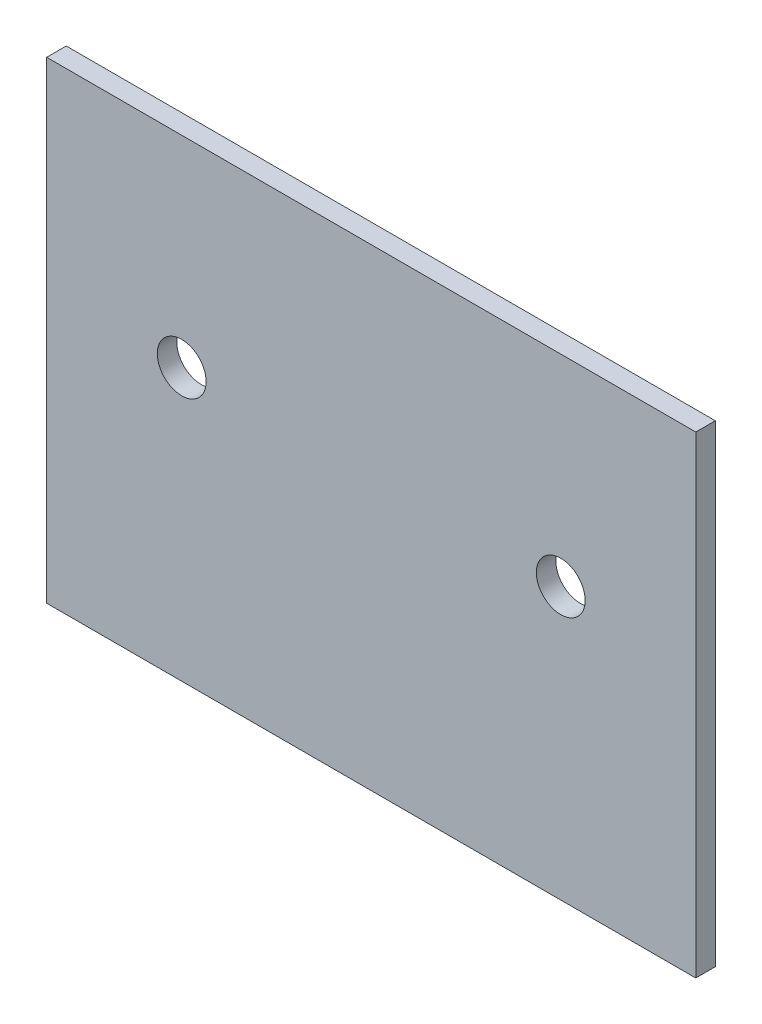
SolidWorks part; units mm, degrees
ref_plane "Front Plane" through (0, 0, 0) normal (0, 0, 1) x (1, 0, 0)
ref_plane "Top Plane" through (0, 0, 0) normal (0, 1, 0) x (1, 0, 0)
ref_plane "Right Plane" through (0, 0, 0) normal (1, 0, 0) x (0, 0, -1)
sketch "Sketch1" plane through (0, 0, 0) normal (0, 0, 1) x (1, 0, 0)
  line L1 (-16.61, 12.1) -> (16.61, 12.1)
  line L2 (-16.61, 12.1) -> (-16.61, -12.1)
  line L3 (-16.61, -12.1) -> (16.61, -12.1)
  line L4 (16.61, 12.1) -> (16.61, -12.1)
  line L5 (-16.61, 12.1) -> (16.61, -12.1) construction
  line L6 (-16.61, -12.1) -> (16.61, 12.1) construction
  point P0 (0, 0)
  dimension "D1" = 33.22
  dimension "D2" = 24.2
extrude "Boss-Extrude1" add sketch "Sketch1" along normal blind 1
sketch "Sketch2" plane through (0, 0, 1) normal (0, 0, 1) x (1, 0, 0)
  line L0 (-16.61, -12.1) -> (16.61, -12.1) construction
  line L1 (0, 4.2772) -> (0, -3.0951) construction
  circle A0 centre (9.7, 1.8) radius 1.25
  circle A1 centre (-9.7, 1.8) radius 1.25
  dimension "D2" = 2.5
  dimension "D1" = 13.9
  dimension "D3" = 19.4
extrude "Cut-Extrude1" cut sketch "Sketch2" against normal blind 1
